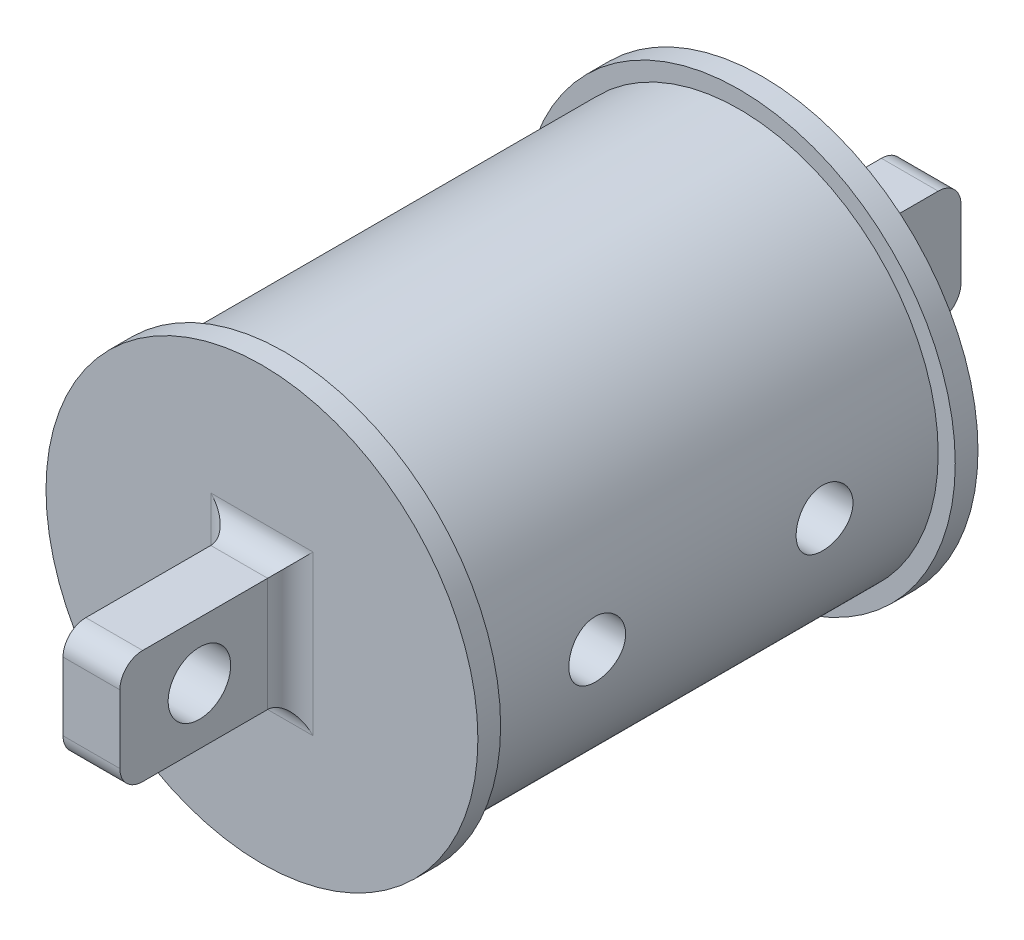
SolidWorks part; units mm, degrees
ref_plane "Front Plane" through (0, 0, 0) normal (0, 0, 1) x (1, 0, 0)
ref_plane "Top Plane" through (0, 0, 0) normal (0, 1, 0) x (1, 0, 0)
ref_plane "Right Plane" through (0, 0, 0) normal (1, 0, 0) x (0, 0, -1)
sketch "Sketch1" plane through (0, 0, 0) normal (0, 0, 1) x (1, 0, 0)
  circle A0 centre (0, 0) radius 22.225
  dimension "D1" = 44.45
extrude "Boss-Extrude1" add sketch "Sketch1" along normal mid plane 50.8
sketch "Sketch2" plane through (0, 0, 25.4) normal (0, 0, 1) x (1, 0, 0)
  circle A0 centre (0, 0) radius 24.13
  dimension "D1" = 48.26
extrude "Boss-Extrude2" add sketch "Sketch2" along normal blind 2.54
sketch "Sketch3" plane through (0, 0, 27.94) normal (0, 0, 1) x (1, 0, 0)
  line L1 (-3.175, -6.35) -> (3.175, -6.35)
  line L2 (-3.175, -6.35) -> (-3.175, 6.35)
  line L3 (-3.175, 6.35) -> (3.175, 6.35)
  line L4 (3.175, -6.35) -> (3.175, 6.35)
  line L5 (-3.175, -6.35) -> (3.175, 6.35) construction
  line L6 (-3.175, 6.35) -> (3.175, -6.35) construction
  point P0 (0, 0)
  dimension "D1" = 6.35
  dimension "D2" = 12.7
extrude "Boss-Extrude3" add sketch "Sketch3" along normal blind 19.05
sketch "Sketch4" plane through (3.175, 0, 0) normal (1, 0, 0) x (0, 0, -1)
  line L0 (-38.1, 0) -> (-27.94, 0) construction
  line L1 (-27.94, -6.35) -> (-27.94, 6.35) construction
  line L3 (0, 26.543) -> (0, -26.543) construction
  circle A0 centre (-38.1, 0) radius 3.4925
  dimension "D1" = 6.985
  dimension "D2" = 38.1
extrude "Cut-Extrude1" cut sketch "Sketch4" against normal through all
fillet "Fillet1" radius 2.54 6 edges at (0, -6.35, 27.94) (0, 6.35, 27.94) (0, -6.35, 46.99) (0, 6.35, 46.99) (-3.175, 0, 27.94) (3.175, 0, 27.94)
mirror "Mirror1" about plane through (0, 0, 0) normal (0, 0, 1) of "Fillet1", "Cut-Extrude1", "Boss-Extrude3", "Boss-Extrude2"
sketch "Sketch5" plane through (0, 0, 0) normal (1, 0, 0) x (0, 0, -1)
  line L0 (26.543, 0) -> (-26.543, 0) construction
  line L1 (0, 26.543) -> (0, -26.543) construction
  circle A0 centre (-12.7, 0) radius 3.175
  circle A1 centre (12.7, 0) radius 3.175
  dimension "D1" = 6.35
  dimension "D2" = 6.35
  dimension "D3" = 12.7
  dimension "D4" = 12.7
extrude "Cut-Extrude2" cut sketch "Sketch5" against normal through all both and the other way through all
